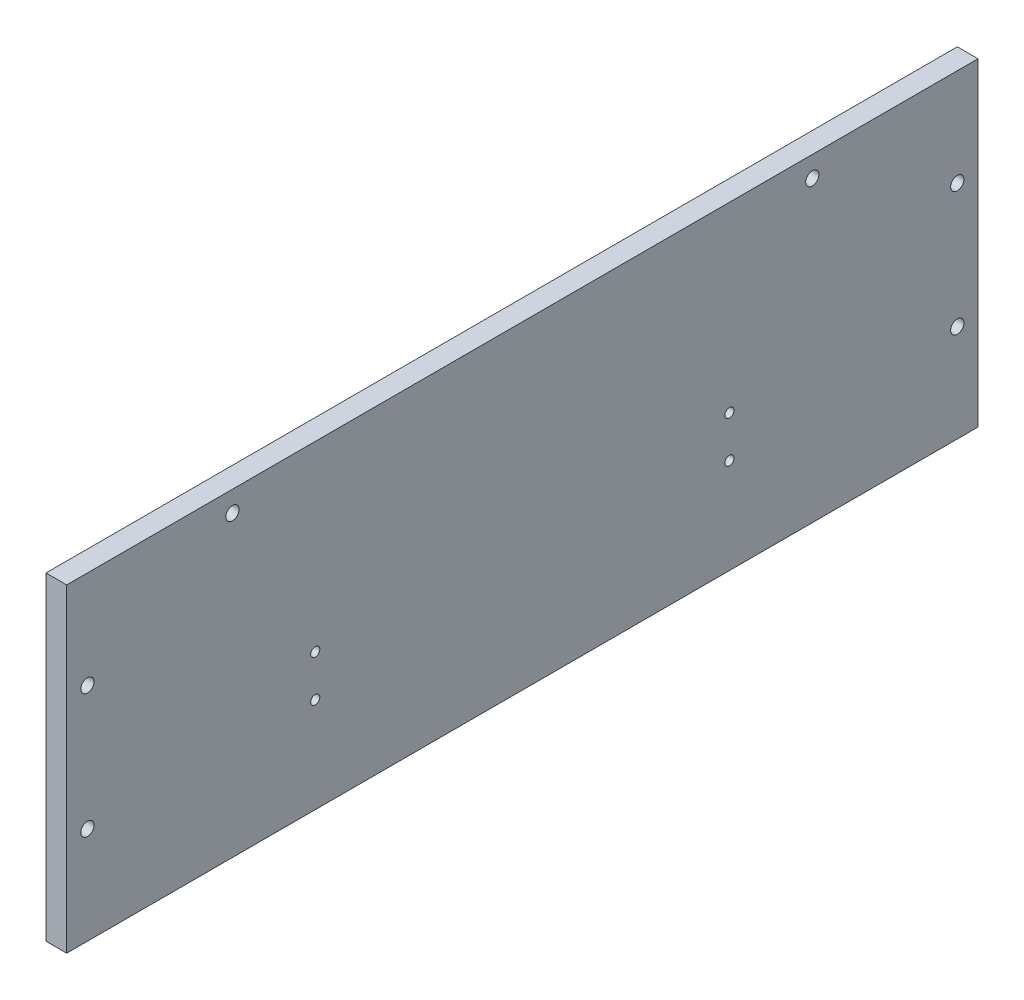
SolidWorks part; units mm, degrees
material "Polywood"
ref_plane "Front Plane" through (0, 0, 0) normal (0, 0, 1) x (1, 0, 0)
ref_plane "Top Plane" through (0, 0, 0) normal (0, 1, 0) x (1, 0, 0)
ref_plane "Right Plane" through (0, 0, 0) normal (1, 0, 0) x (0, 0, -1)
sketch "Sketch1" plane through (0, 0, 0) normal (1, 0, 0) x (0, 0, -1)
  line L0 (0, 0) -> (0, 50000) construction
  line L1 (-110, 0) -> (-115, 0)
  line L2 (-110, 0) -> (-110, 110)
  line L3 (-110, 110) -> (-115, 110)
  line L4 (-115, 0) -> (-115, 110)
  line L5 (115, 0) -> (115, 110)
  line L6 (110, 110) -> (115, 110)
  line L7 (110, 0) -> (110, 110)
  line L8 (110, 0) -> (115, 0)
  dimension "D1" = 110
  dimension "D2" = 5
  dimension "D3" = 110
extrude "Boss-Extrude1" add sketch "Sketch1" along normal blind 120 and the other way blind 110
sketch "Sketch2" plane through (-110, 0, 0) normal (-1, 0, 0) x (0, 0, 1)
  line L0 (-110, 110) -> (-110, 0) construction
  line L1 (-115, 0) -> (-110, 0)
  line L2 (-115, 0) -> (-115, 37)
  line L3 (-115, 37) -> (-110, 37)
  line L4 (-110, 0) -> (-110, 37)
  line L5 (0, 0) -> (0, 50000) construction
  line L6 (110, 0) -> (110, 37)
  line L7 (115, 37) -> (110, 37)
  line L8 (115, 0) -> (115, 37)
  line L9 (115, 0) -> (110, 0)
  dimension "D1" = 37
extrude "Boss-Extrude2" add sketch "Sketch2" along normal blind 50
sketch "Sketch3" plane through (-160, 0, 0) normal (-1, 0, 0) x (0, 0, 1)
  line L5 (110, 37) -> (110, 0) construction
  line L6 (-110, 37) -> (110, 37)
  line L7 (-110, 37) -> (-110, 32)
  line L8 (-110, 32) -> (110, 32)
  line L9 (110, 37) -> (110, 32)
  dimension "D1" = 5
extrude "Boss-Extrude3" add sketch "Sketch3" against normal blind 50
sketch "Sketch4" plane through (-110, 0, 0) normal (-1, 0, 0) x (0, 0, 1)
  line L1 (-115, 110) -> (115, 110)
  line L2 (-115, 110) -> (-115, 37)
  line L3 (-115, 37) -> (115, 37)
  line L4 (115, 110) -> (115, 37)
extrude "Boss-Extrude6" add sketch "Sketch4" along normal blind 5
fillet "Fillet3" [suppressed] radius 15
ref_plane "Plane1" through (115, 115, 0) normal (-0.7071, -0.7071, 0) x (0, 0, 1)
sketch "Sketch9" plane through (0, 0, 115) normal (0, 0, 1) x (1, 0, 0)
  line L0 (120, 110) -> (116.4645, 106.4645)
  line L1 (116.4645, 106.4645) -> (120, 102.9289)
  line L2 (120, 110) -> (120, 0) construction
  line L3 (120, 102.9289) -> (120, 110)
  dimension "D1" = 5
  dimension "D2" = 45
extrude "Cut-Extrude3" cut sketch "Sketch9" against normal through all
sketch "Sketch5" plane through (115, 115, 0) normal (-0.7071, -0.7071, 0) x (0, 0, 1)
  line L0 (-115, -7.0711) -> (-110, -7.0711) construction
  line L1 (174, -7.0711) -> (-174, -7.0711)
  line L2 (174, -7.0711) -> (174, -234.0711)
  line L3 (174, -234.0711) -> (-174, -234.0711)
  line L4 (-174, -7.0711) -> (-174, -234.0711)
  line L6 (164, -17.0711) -> (-164, -17.0711)
  line L7 (164, -17.0711) -> (164, -224.0711)
  line L8 (164, -224.0711) -> (-164, -224.0711)
  line L9 (-164, -17.0711) -> (-164, -224.0711)
  point P8 (0, -7.0711)
  dimension "D1" = 227
  dimension "D2" = 348
  dimension "D3" = 10
  dimension "D4" = 10
  dimension "D5" = 207
  dimension "D6" = 328
extrude "Boss-Extrude7" add sketch "Sketch5" along normal blind 5 separate body
sketch "Sketch10" plane through (0, 0, 115) normal (0, 0, 1) x (1, 0, 0)
  line L0 (120, 110) -> (111.4645, 110)
  line L1 (-115, 110) -> (120, 110) construction
  line L2 (111.4645, 110) -> (111.4645, 0)
  line L3 (-160, 0) -> (120, 0) construction
  line L4 (111.4645, 0) -> (120, 0)
  line L5 (120, 0) -> (120, 102.9289)
  line L6 (276.9777, -54.0488) -> (116.4645, 106.4645) construction
  line L7 (120, 102.9289) -> (120, 0) construction
  line L8 (120, 102.9289) -> (116.4645, 106.4645)
  line L9 (116.4645, 106.4645) -> (120, 110)
  dimension "D1" = 5
extrude "Boss-Extrude8" add sketch "Sketch10" along normal blind 59
mirror "Mirror3" about plane through (0, 0, 0) normal (0, 0, 1) of "Boss-Extrude8"
fillet "Fillet5" radius 15 2 edges at (111.4645, 55, -115) (111.4645, 55, 115)
sketch "Sketch12" plane through (0, 0, 174) normal (0, 0, 1) x (1, 0, 0)
  line L0 (120, 0) -> (222.9289, 0)
  line L1 (276.9777, -54.0488) -> (116.4645, 106.4645) construction
  line L2 (222.9289, 0) -> (120, 102.9289)
  line L3 (120, 102.9289) -> (120, 0)
extrude "Boss-Extrude9" add sketch "Sketch12" against normal blind 5 separate body
sketch "Sketch13" plane through (0, 0, -174) normal (0, 0, -1) x (-1, 0, 0)
  line L0 (-120, 102.9289) -> (-120, 0)
  line L1 (-120, 0) -> (-222.9289, 0)
  line L2 (-116.4645, 106.4645) -> (-276.9777, -54.0488) construction
  line L3 (-120, 0) -> (-222.9289, 0) construction
  line L4 (-222.9289, 0) -> (-120, 102.9289)
extrude "Boss-Extrude10" add sketch "Sketch13" against normal blind 5 separate body
fillet "Fillet6" radius 3 2 edges at (111.4645, 55, 174) (111.4645, 55, -174)
sketch "Sketch14" plane through (0, 110, 0) normal (0, 1, 0) x (1, 0, 0)
  line L0 (-110, -110) -> (-110, 110) construction
  line L5 (-115, -115) -> (-115, 115) construction
  line L11 (-110, 193.7612) -> (-110, -200.6021)
  line L12 (-115, 193.7612) -> (-217.0873, 193.7612)
  line L15 (-110, 193.7612) -> (365.2233, 193.7612)
  line L16 (365.2233, 105) -> (365.2233, 193.7612)
  line L19 (-110, -200.6021) -> (365.2233, -200.6021)
  line L20 (365.2233, -115) -> (365.2233, -200.6021)
  line L22 (365.2233, 105) -> (365.2233, -115)
  line L26 (-115, 193.7612) -> (-115, -200.6021)
  line L27 (-115, -200.6021) -> (-217.0873, -200.6021)
  line L28 (-217.0873, 193.7612) -> (-217.0873, -200.6021)
extrude "Cut-Extrude4" cut sketch "Sketch14" against normal through all
sketch "Sketch16" plane through (-115, 0, 0) normal (-1, 0, 0) x (0, 0, 1)
  line L0 (115, 0) -> (115, 110) construction
  line L1 (-115, 0) -> (115, 0)
  line L2 (-115, 0) -> (-115, 32)
  line L3 (-110, 33) -> (110, 33)
  line L4 (115, 0) -> (115, 32)
  line L6 (115, 110) -> (-115, 110) construction
  line L8 (-115, 32) -> (-115, 110)
  line L9 (-115, 110) -> (-110, 110)
  line L10 (-110, 33) -> (-110, 110)
  line L11 (-110, 0) -> (-110, 32) construction
  line L12 (110, 32) -> (110, 0) construction
  line L13 (115, 110) -> (110, 110)
  line L14 (115, 110) -> (115, 32)
  line L16 (110, 110) -> (110, 33)
  line L17 (-110, 32) -> (110, 32) construction
  dimension "D1" = 1
extrude "Cut-Extrude7" cut sketch "Sketch16" against normal through all
sketch "Sketch17" plane through (-115, 0, 0) normal (-1, 0, 0) x (0, 0, 1)
  line L1 (64.9548, 61) -> (-49935.0452, 61) construction
  line L2 (0, 0) -> (0, 50000) construction
  line L3 (110, 33) -> (-110, 33) construction
  circle A0 centre (50, 66) radius 1.1
  circle A1 centre (50, 56) radius 1.1
  circle A2 centre (-50, 56) radius 1.1
  circle A3 centre (-50, 66) radius 1.1
  dimension "D2" = 2.2
  dimension "D1" = 23
  dimension "D3" = 5
  dimension "D4" = 50
extrude "Holes for part 4" cut sketch "Sketch17" against normal through all
sketch "Sketch18" plane through (-115, 0, 0) normal (-1, 0, 0) x (0, 0, 1)
  line L0 (110, 71.5) -> (-49890, 71.5) construction
  line L1 (110, 110) -> (110, 33) construction
  line L2 (0, 33) -> (0, 50033) construction
  line L3 (110, 33) -> (-110, 33) construction
  line L4 (110, 110) -> (-110, 110) construction
  circle A0 centre (105, 56.5) radius 1.6
  circle A1 centre (105, 86.5) radius 1.6
  circle A2 centre (-105, 86.5) radius 1.6
  circle A3 centre (-105, 56.5) radius 1.6
  circle A4 centre (70, 105) radius 1.6
  circle A5 centre (-70, 105) radius 1.6
  point P6 (110, 71.5)
  point P11 (0, 33)
  dimension "D1" = 3.2
  dimension "D4" = 3.2
  dimension "D2" = 5
  dimension "D3" = 15
  dimension "D5" = 5
  dimension "D6" = 70
extrude "Cut-Extrude9" cut sketch "Sketch18" against normal through all
